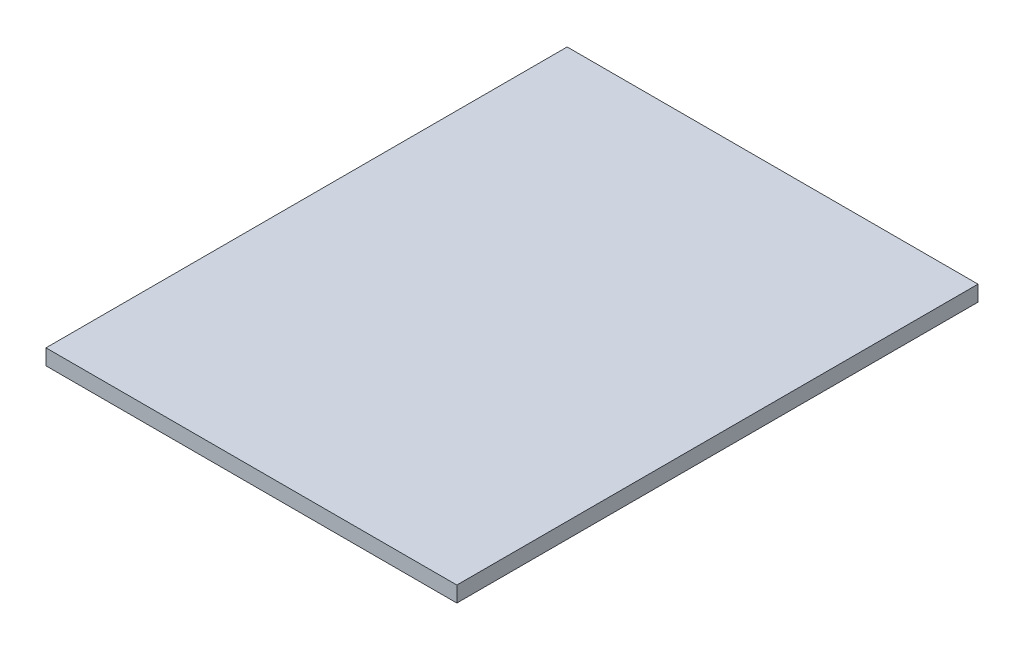
SolidWorks part; units mm, degrees
ref_plane "Спереди" through (0, 0, 0) normal (0, 0, 1) x (1, 0, 0)
ref_plane "Сверху" through (0, 0, 0) normal (0, 1, 0) x (1, 0, 0)
ref_plane "Справа" through (0, 0, 0) normal (1, 0, 0) x (0, 0, -1)
sketch "Эскиз1" plane through (0, 0, 0) normal (0, 1, 0) x (1, 0, 0)
  line L1 (0, 0) -> (473, 0)
  line L2 (0, 0) -> (0, 600)
  line L3 (0, 600) -> (473, 600)
  line L4 (473, 0) -> (473, 600)
  dimension "D1" = 473
  dimension "D2" = 600
extrude "Бобышка-Вытянуть1" add sketch "Эскиз1" along normal blind 18
